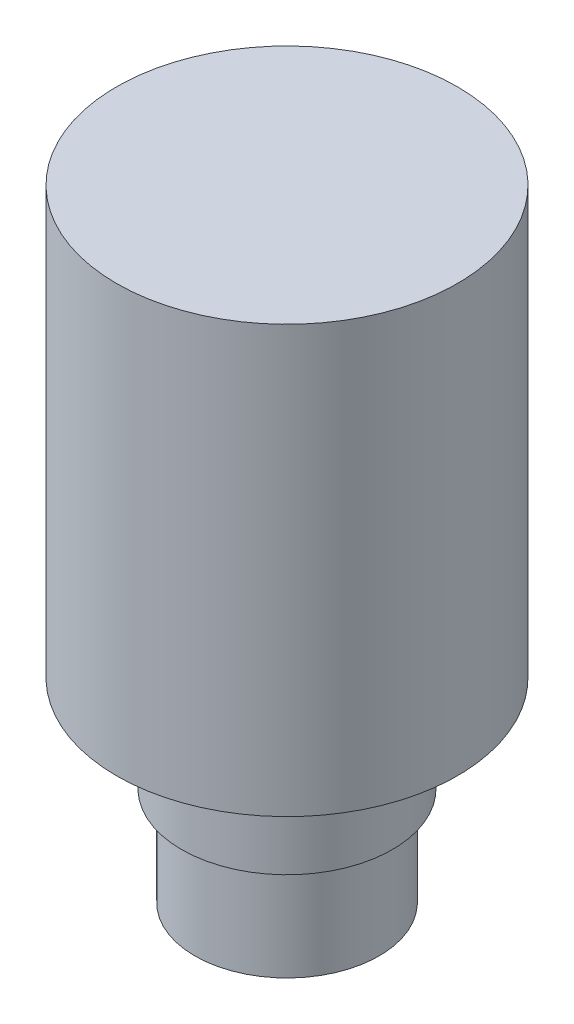
SolidWorks part; units mm, degrees
material "PVC Rigid"
ref_plane "Front Plane" through (0, 0, 0) normal (0, 0, 1) x (1, 0, 0)
ref_plane "Top Plane" through (0, 0, 0) normal (0, 1, 0) x (1, 0, 0)
ref_plane "Right Plane" through (0, 0, 0) normal (1, 0, 0) x (0, 0, -1)
sketch "Sketch1" plane through (0, 0, 0) normal (1, 0, 0) x (0, 0, -1)
  line L0 (0, 0) -> (0, 131.064)
  line L1 (0, 131.064) -> (35.941, 131.064)
  line L2 (35.941, 131.064) -> (35.941, 41.148)
  line L3 (35.941, 41.148) -> (19.431, 41.148)
  line L4 (19.431, 41.148) -> (19.431, 34.798)
  line L5 (19.431, 0) -> (0, 0)
  line L6 (19.431, 34.798) -> (22.225, 34.798)
  line L7 (22.225, 34.798) -> (22.225, 20.828)
  line L8 (22.225, 20.828) -> (19.431, 20.828)
  line L9 (19.431, 20.828) -> (19.431, 0)
  point P9 (20.828, 20.828)
  dimension "D1" = 19.431
  dimension "D2" = 35.941
  dimension "D3" = 41.148
  dimension "D4" = 89.916
  dimension "D5" = 22.225
  dimension "D6" = 20.32
  dimension "D7" = 6.35
revolve "Revolve1" add sketch "Sketch1" angle 360 about L0
